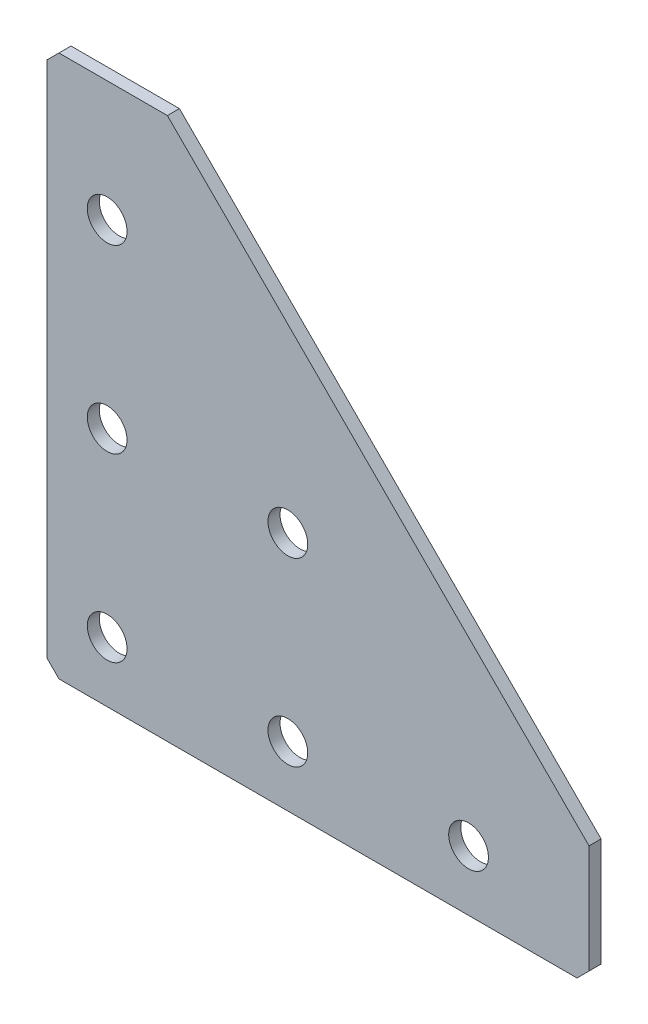
SolidWorks part; units mm, degrees
material "Простая углеродистая сталь"
ref_plane "Спереди(Плоскость XY)" through (0, 0, 0) normal (0, 0, 1) x (1, 0, 0)
ref_plane "Сверху(Плоскость XZ)" through (0, 0, 0) normal (0, 1, 0) x (1, 0, 0)
ref_plane "Справа(Плоскость ZY)" through (0, 0, 0) normal (1, 0, 0) x (0, 0, -1)
sketch "Эскиз1" plane through (0, 0, 0) normal (0, 0, -1) x (1, 0, 0)
  line L0 (0, 0) -> (0, 90)
  line L1 (0, 90) -> (90, 90)
  line L2 (90, 90) -> (90, 70)
  line L3 (90, 70) -> (20, 70) construction
  line L4 (20, 70) -> (20, 0) construction
  line L5 (20, 0) -> (0, 0)
  line L6 (20, 0) -> (90, 70)
  dimension "D1" = 90
  dimension "D3" = 20
extrude "Бобышка-Вытянуть1" add sketch "Эскиз1" along normal blind 2
hole_wizard "Отверстие с зазором M61" positions "Эскиз2" profile "Эскиз3" hole size "M6" standard "DIN" end condition through all
sketch "Эскиз2" plane through (0, 0, -2) normal (0, 0, -1) x (1, 0, 0)
  line L0 (10, 0) -> (10, 90) construction
  line L1 (0, 0) -> (20, 0) construction
  line L2 (90, 90) -> (0, 90) construction
  line L3 (90, 80) -> (0, 80) construction
  line L4 (90, 70) -> (90, 90) construction
  line L5 (0, 90) -> (0, 0) construction
  point P0 (40, 80)
  point P2 (10, 80)
  point P4 (10, 50)
  point P6 (10, 20)
  point P21 (70, 80)
  point P22 (40, 50)
  dimension "D1" = 30
  dimension "D2" = 30
  dimension "D3" = 30
  dimension "D4" = 20
  dimension "D5" = 30
sketch "Эскиз3" plane through (40, -80, -2) normal (1, 0, 0) x (0, 1, 0)
  line L0 (0, 0) -> (0, 2)
  line L1 (0, 2) -> (3.3, 2)
  line L2 (3.3, 2) -> (3.3, 0)
  line L5 (3.3, 0) -> (0, 0)
  line L11 (0, -6.35) -> (0, 107.95) construction
  dimension "Диаметр сквозного отверстия" = 6.6
  dimension "Глубина сквозного отверстия" = 2
chamfer "Фаска1" distance 2 angle 45 3 edges at (0, 0, -1) (90, -90, -1) (0, -90, -1)
